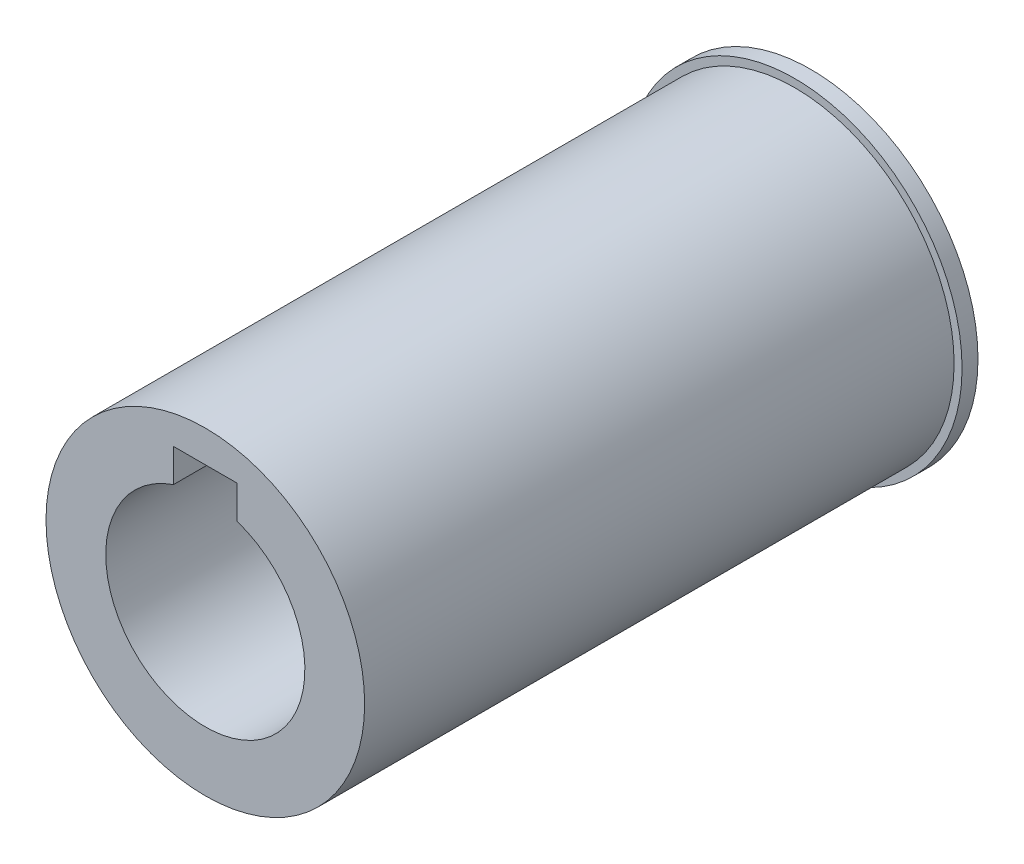
SolidWorks part; units mm, degrees
material "6061 Alloy"
ref_plane "Front Plane" through (0, 0, 0) normal (0, 0, 1) x (1, 0, 0)
ref_plane "Top Plane" through (0, 0, 0) normal (0, 1, 0) x (1, 0, 0)
ref_plane "Right Plane" through (0, 0, 0) normal (1, 0, 0) x (0, 0, -1)
sketch "Sketch1" plane through (0, 0, 0) normal (0, 0, 1) x (1, 0, 0)
  circle A0 centre (0, 0) radius 21
  dimension "D1" = 42
extrude "Boss-Extrude1" add sketch "Sketch1" along normal blind 2
sketch "Sketch2" plane through (0, 0, 2) normal (0, 0, 1) x (1, 0, 0)
  circle A0 centre (0, 0) radius 20
  dimension "D1" = 40
extrude "Boss-Extrude2" add sketch "Sketch2" along normal blind 74
sketch "Sketch3" plane through (0, 0, 0) normal (0, 0, -1) x (-1, 0, 0)
  circle A0 centre (0, 0) radius 12.5
  dimension "D1" = 25
extrude "Cut-Extrude1" cut sketch "Sketch3" against normal through all
sketch "Sketch4" plane through (0, 0, 0) normal (0, 0, -1) x (-1, 0, 0)
  line L0 (0, 1.1) -> (0, -1.1) construction
  line L1 (-4, 9) -> (4, 9)
  line L2 (-4, 9) -> (-4, 16)
  line L3 (-4, 16) -> (4, 16)
  line L4 (4, 9) -> (4, 16)
  line L5 (-4, 9) -> (4, 16) construction
  line L6 (-4, 16) -> (4, 9) construction
  circle A0 centre (0, 0) radius 12.5 construction
  point P0 (0, 12.5)
  dimension "D1" = 7
  dimension "D2" = 8
extrude "Cut-Extrude2" cut sketch "Sketch4" against normal up to surface (76 mm away) up to face at (-12.5, 0, 76)
ref_plane "Plane1" through (0, 0, 28) normal (0, 0, 1) x (1, 0, 0)
ref_plane "Plane2" through (0, -20, 0) normal (0, -1, 0) x (-1, 0, 0)
hole_wizard "M6x1.0 Tapped Hole1" positions "Sketch6" profile "Sketch7" tap size "M6x1.0" standard "ANSI Metric"
sketch "Sketch6" plane through (0, -20, 0) normal (0, -1, 0) x (-1, 0, 0)
  line L0 (0, 23.1) -> (0, -23.1) construction
  line L1 (-20, -76) -> (20, -76) construction
  point P0 (0, -56)
  dimension "D1" = 20
sketch "Sketch7" plane through (0, -20, 56) normal (1, 0, 0) x (0, 0, -1)
  line L0 (0, 0) -> (0, 10)
  line L1 (0, 10) -> (2.5, 8.4978)
  line L2 (2.5, 8.4978) -> (2.5, 0)
  line L5 (2.5, 0) -> (0, 0)
  line L10 (0, 10) -> (-2.5, 8.4978) construction
  line L11 (0, -6.35) -> (0, 107.95) construction
  dimension "Tap Drill Dia." = 5
  dimension "Tap Drill Depth" = 10
  dimension "Drill Angle" = 118
cosmetic thread "Hole Thread1" parameters "D1"=7.7526, "D2"=6
